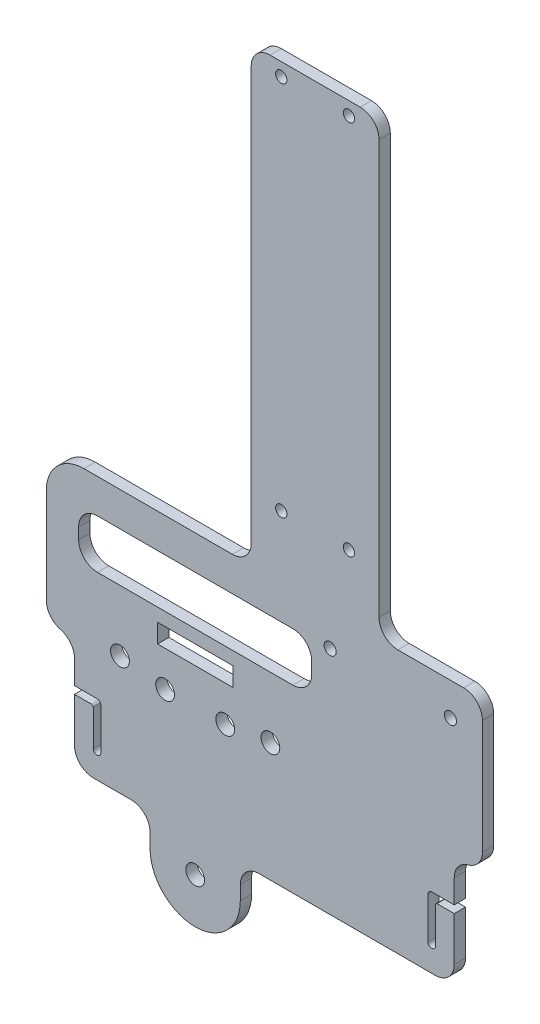
SolidWorks part; units mm, degrees
material "2024 Alloy"
ref_plane "Front Plane" through (0, 0, 0) normal (0, 0, 1) x (1, 0, 0)
ref_plane "Top Plane" through (0, 0, 0) normal (0, 1, 0) x (1, 0, 0)
ref_plane "Right Plane" through (0, 0, 0) normal (1, 0, 0) x (0, 0, -1)
sketch "Sketch1" plane through (0, 0, 0) normal (0, 0, 1) x (1, 0, 0)
  line L1 (-100, 150) -> (100, 150)
  line L2 (-100, 150) -> (-100, -150)
  line L3 (-100, -150) -> (100, -150)
  line L4 (100, 150) -> (100, -150)
  line L5 (-100, 150) -> (100, -150) construction
  line L6 (-100, -150) -> (100, 150) construction
  line L11 (100, 150) -> (-58.5274, 150)
  line L12 (100, 150) -> (100, 170)
  line L13 (100, 170) -> (-58.5274, 170)
  line L14 (-58.5274, 150) -> (-58.5274, 170)
  point P0 (0, 0)
  dimension "D1" = 300
  dimension "D2" = 200
  dimension "D3" = 20
extrude "Boss-Extrude1" add sketch "Sketch1" along normal blind 3 contours L4 L1 L2 L3 | L14 L1 L12 L13
sketch "Sketch2" plane through (0, 0, 3) normal (0, 0, 1) x (1, 0, 0)
  line L0 (56.5, -1.25) -> (49.5, -1.25)
  line L1 (-44.5, 23.75) -> (44.5, 23.75) construction
  line L2 (-44.5, 23.75) -> (-44.5, -23.75) construction
  line L3 (-44.5, -23.75) -> (44.5, -23.75) construction
  line L4 (44.5, 23.75) -> (44.5, -23.75) construction
  line L5 (-44.5, 23.75) -> (44.5, -23.75) construction
  line L6 (-44.5, -23.75) -> (44.5, 23.75) construction
  line L7 (49.5, -1.25) -> (49.5, -13.25)
  line L8 (49.5, -13.25) -> (51.5, -13.25)
  line L9 (51.5, -13.25) -> (51.5, -3.25)
  line L10 (51.5, -3.25) -> (56.5, -3.25)
  line L11 (56.5, -3.25) -> (56.5, -1.25)
  line L13 (-39.5, -3.25) -> (-44.5, -3.25)
  line L14 (-39.5, -13.25) -> (-39.5, -3.25)
  line L15 (-37.5, -13.25) -> (-39.5, -13.25)
  line L16 (-37.5, -1.25) -> (-37.5, -13.25)
  line L17 (-44.5, -1.25) -> (-37.5, -1.25)
  line L18 (-44.5, -3.25) -> (-44.5, -1.25)
  circle A0 centre (-32.4, 11.65) radius 4.6
  circle A1 centre (7.6, 11.65) radius 4.6
  circle A2 centre (-12.4, -28.75) radius 5
  circle A3 centre (-32.4, 11.65) radius 2.5
  circle A4 centre (7.6, 11.65) radius 2.5
  circle A5 centre (-12.4, -28.75) radius 2.5
  arc A6 (51.5, -13.25) -> (49.5, -13.25) centre (50.5, -13.25) cw
  arc A7 (56.5, -1.25) -> (56.5, -3.25) centre (56.5, -2.25) cw
  arc A8 (-44.5, -1.25) -> (-44.5, -3.25) centre (-44.5, -2.25) ccw
  arc A9 (-37.5, -13.25) -> (-39.5, -13.25) centre (-38.5, -13.25) cw
  point P0 (0, 0)
  dimension "D3" = 9.2
  dimension "D4" = 12.1
  dimension "D5" = 12.1
  dimension "D6" = 9.2
  dimension "D7" = 40
  dimension "D8" = 10
  dimension "D10" = 5
  dimension "D17" = 40.4
  dimension "D1" = 89
  dimension "D2" = 47.5
  dimension "D9" = 20
  dimension "D11" = 25
  dimension "D12" = 7
  dimension "D13" = 12
  dimension "D14" = 2
  dimension "D15" = 2
  dimension "D16" = 5
  dimension "D18" = 12
extrude "Cut-Extrude1" cut sketch "Sketch2" against normal blind 5 contours A5 | A4 | A3 | L18 L13 L14 L15 L16 L17 | L10 L11 L0 L7 L8 L9 | L18 A8 | A9 L15 | A6 L8 | A7 L11
sketch "Sketch4" plane through (0, 0, 3) normal (0, 0, 1) x (1, 0, 0)
  line L0 (-44.5, -1.25) -> (-44.5, -20)
  line L1 (-44.5, -1.25) -> (-44.5, 10)
  line L2 (37, 165) -> (37, 77) construction
  line L4 (53, 170) -> (26, 170) construction
  line L5 (42, 165) -> (42, 77) construction
  line L6 (100, 170) -> (-58.5274, 170) construction
  line L7 (53, 170) -> (53, -20) construction
  line L8 (53, -20) -> (-0.4, -20)
  line L9 (-0.4, -28.75) -> (-0.4, -20)
  line L10 (-100, -150) -> (100, -150) construction
  line L11 (-24.4, -28.75) -> (-24.4, -20)
  line L12 (-52, -20) -> (-24.4, -20)
  line L13 (56.5, -20) -> (53, -20)
  line L17 (-44.5, 10) -> (-52, 10)
  line L18 (100, 170) -> (100, -150) construction
  line L19 (56.5, -3.25) -> (56.5, -20)
  line L20 (-52, 50) -> (2.5, 50)
  line L21 (-52, 50) -> (-52, -20)
  line L22 (-100, 150) -> (-100, -150) construction
  line L23 (56.5, -1.25) -> (56.5, 10)
  line L25 (56.5, 10) -> (64, 10)
  line L26 (26, 170) -> (26, 50) construction
  line L28 (53, 50) -> (64, 50)
  line L29 (64, 10) -> (64, 50)
  line L30 (37, 165) -> (42, 165) construction
  line L31 (19.5, 185.2659) -> (19.5, 39.6962) construction
  line L32 (2.5, 50) -> (2.5, 170)
  line L33 (2.5, 170) -> (36.5, 170) construction
  line L34 (36.5, 170) -> (36.5, 50)
  line L35 (36.5, 50) -> (53, 50)
  line L36 (2.5, 164) -> (36.5, 164)
  line L37 (56.5, -3.25) -> (56.5, -1.25)
  arc A2 (37, 77) -> (42, 77) centre (39.5, 77) ccw construction
  circle A3 centre (-12.4, -28.75) radius 12
  arc A4 (-44.5, -1.25) -> (-44.5, -3.25) centre (-44.5, -2.25) ccw construction
  circle A5 centre (39.5, 77) radius 4 construction
  point P50 (39.5, 165)
  point P51 (19.5, 170)
  dimension "D1" = 130
  dimension "D13" = 8
  dimension "D16" = 24
  dimension "D2" = 47
  dimension "D3" = 48
  dimension "D4" = 126
  dimension "D5" = 11
  dimension "D6" = 20
  dimension "D7" = 30
  dimension "D8" = 70
  dimension "D9" = 5
  dimension "D10" = 40
  dimension "D11" = 11
  dimension "D12" = 5
  dimension "D14" = 17
  dimension "D15" = 114
extrude "Cut-Extrude3" cut sketch "Sketch4" against normal blind 10
sketch "Sketch5" plane through (0, 0, 3) normal (0, 0, 1) x (1, 0, 0)
  line L0 (-43.4, 40.9093) -> (-43.4, 27.9093)
  line L1 (-12.4, 63.5894) -> (-12.4, 7.0443) construction
  line L3 (-43.4, 27.9093) -> (18.6, 27.9093)
  line L5 (18.6, 27.9093) -> (18.6, 40.9093)
  line L7 (18.6, 40.9093) -> (-43.4, 40.9093)
  circle A1 centre (-32.4, 11.65) radius 2.5 construction
  dimension "D3" = 20
  dimension "D1" = 13
  dimension "D2" = 62
extrude "Cut-Extrude4" cut sketch "Sketch5" against normal up to next
fillet "Fillet2" radius 5 4 edges at (18.6, 27.9093, 1.5) (-43.4, 27.9093, 1.5) (-43.4, 40.9093, 1.5) (18.6, 40.9093, 1.5)
fillet "Fillet3" radius 10 1 edges at (-52, 50, 1.5)
fillet "Fillet4" radius 5 9 edges at (-24.4, -20, 1.5) (64, 50, 1.5) (-44.5, -20, 1.5) (36.5, 50, 1.5) (2.5, 50, 1.5) (-44.5, 10, 1.5) (-0.4, -20, 1.5) (56.5, 10, 1.5) (56.5, -20, 1.5)
sketch "Sketch7" plane through (0, 0, 3) normal (0, 0, 1) x (1, 0, 0)
  line L0 (64, 10) -> (64, 45) construction
  line L2 (61.5, 10) -> (64, 10) construction
  circle A0 centre (55.5, 41.3) radius 1.6
  circle A1 centre (23.5, 41.3) radius 1.6
  dimension "D1" = 3.2
  dimension "D4" = 31.3
  dimension "D2" = 8.5
  dimension "D3" = 32
extrude "Cut-Extrude6" cut sketch "Sketch7" against normal up to next
sketch "Sketch8" plane through (0, 0, 3) normal (0, 0, 1) x (1, 0, 0)
  line L0 (-34.482, 21.9093) -> (10.8836, 21.9093) construction
  line L1 (-38.4, 27.9093) -> (13.6, 27.9093) construction
  line L2 (-12.4, -28.75) -> (-12.4, 23.6211) construction
  line L3 (-21.5271, 9.9093) -> (-6.8794, 9.9093) construction
  line L4 (-22.4, 24.4093) -> (-2.4, 24.4093)
  line L5 (-22.4, 24.4093) -> (-22.4, 19.4093)
  line L6 (-22.4, 19.4093) -> (-2.4, 19.4093)
  line L7 (-2.4, 24.4093) -> (-2.4, 19.4093)
  line L8 (-22.4, 24.4093) -> (-2.4, 19.4093) construction
  line L9 (-22.4, 19.4093) -> (-2.4, 24.4093) construction
  circle A2 centre (-12.4, 14.9093) radius 2.5 construction
  circle A3 centre (-4.4, 9.9093) radius 2.5
  circle A4 centre (-20.4, 9.9093) radius 2.5
  point P7 (-12.4, 21.9093)
  dimension "D2" = 20
  dimension "D8" = 5
  dimension "D1" = 6
  dimension "D3" = 5
  dimension "D4" = 7
  dimension "D5" = 18
  dimension "D6" = 8
  dimension "D7" = 8
extrude "Cut-Extrude7" cut sketch "Sketch8" against normal up to next
fillet "Fillet6" radius 1 2 edges at (49.5, -1.25, 1.5) (-37.5, -1.25, 1.5)
fillet "Fillet7" radius 0.5 2 edges at (-39.5, -3.25, 1.5) (51.5, -3.25, 1.5)
sketch "Sketch9" plane through (0, 0, 3) normal (0, 0, 1) x (1, 0, 0)
  line L0 (19.5, 176.6767) -> (19.5, 56.4007) construction
  line L1 (36.5, 170) -> (2.5, 170) construction
  circle A0 centre (10.5, 166.5) radius 1.5
  circle A1 centre (10.5, 66.5) radius 1.5
  circle A2 centre (28.5, 166.5) radius 1.5
  circle A3 centre (28.5, 66.5) radius 1.5
  point P4 (19.5, 170)
  dimension "D1" = 3
  dimension "D3" = 9
  dimension "D4" = 3
  dimension "D2" = 3.5
  dimension "D5" = 100
extrude "Cut-Extrude8" cut sketch "Sketch9" against normal blind 10
fillet "Fillet8" radius 5 4 edges at (2.5, 170, 1.5) (36.5, 170, 1.5) (-52, 10, 1.5) (64, 10, 1.5)
